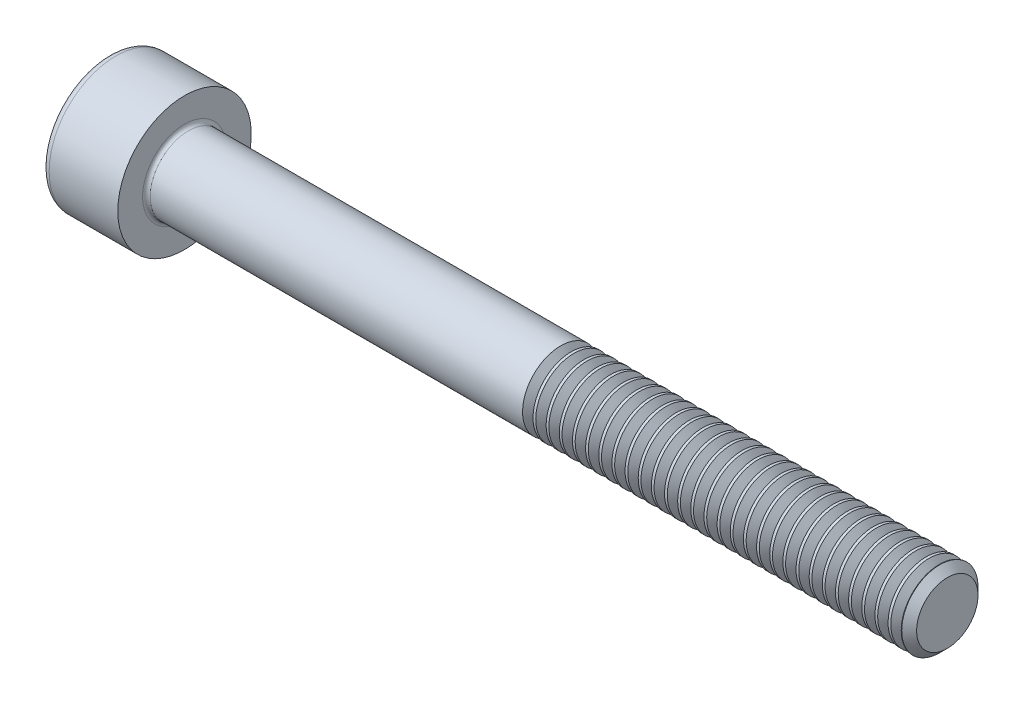
SolidWorks part; units mm, degrees
revolve "Base-Revolve" add sketch "BodySke"
sketch "BodySke" plane through (0, 0, 0) normal (0, 0, 1) x (1, 0, 0)
  line L0 (0, 0) -> (0, 3.5)
  line L1 (0, 3.5) -> (4, 3.5)
  line L2 (4, 3.5) -> (4, 2)
  line L3 (4, 2) -> (43.61, 2)
  line L4 (44, 1.61) -> (44, 0)
  line L5 (44, 0) -> (0, 0)
  line L6 (-31.75, 0) -> (127, 0) construction
  line L8 (44, 1.61) -> (43.61, 2)
  line L10 (44, -1.61) -> (43.61, -2) construction
  line L11 (4.7, 9.525) -> (4.7, 3.175) construction
  line L12 (24, 9.525) -> (24, 3.175) construction
  line L13 (-16, 9.525) -> (-16, 3.175) construction
cosmetic thread "ThreadCosmetic" [suppressed]
fillet "Fillet1" radius 0.2 1 edges at (4, 0, 2)
fillet "Fillet2" radius 0.4 1 edges at (0, 0, 3.5)
ref_plane "Plane1" through (0, 0, 0) normal (0, 0, 1) x (1, 0, 0)
ref_plane "Plane2" through (0, 0, 0) normal (0, 1, 0) x (1, 0, 0)
ref_plane "Plane3" through (0, 0, 0) normal (1, 0, 0) x (0, 0, -1)
sketch "Sketch2" plane through (0, 0, 0) normal (0, 0, 1) x (1, 0, 0)
  line L0 (0, 1.51) -> (2, 1.51)
  line L1 (2, 1.51) -> (2.8718, 0)
  line L2 (-31.75, 0) -> (127, 0) construction
  line L3 (2.8718, 0) -> (0, 0)
  line L4 (0, 0) -> (0, 1.51)
  line L6 (0, 0) -> (47.625, 0) construction
revolve "Hex-PreBroach" cut sketch "Sketch2" angle 360 about L6
sketch "Sketch3" plane through (0, 0, 0) normal (-1, 0, 0) x (0, 0.5, 0.866)
  line L0 (0.8718, 1.51) -> (-0.8718, 1.51)
  line L1 (-0.8718, 1.51) -> (-1.7436, 0)
  line L2 (0.8718, 1.51) -> (1.7436, 0)
  line L3 (0.8718, -1.51) -> (1.7436, 0)
  line L4 (0.8718, -1.51) -> (-0.8718, -1.51)
  line L5 (-0.8718, -1.51) -> (-1.7436, 0)
extrude "Hex" cut sketch "Sketch3" against normal blind 2
sketch "ThdSchSke" plane through (0, 0, 0) normal (0, 0, 1) x (1, 0, 0)
  line L0 (24, -1.61) -> (23.7269, -2)
  line L1 (24, -1.61) -> (24.2731, -2)
  line L2 (24.2731, -2) -> (24.2731, -2.5)
  line L3 (-3.175, 0) -> (5.1513, 0) construction
  line L4 (0, 3.1) -> (0, -3.1) construction
  line L5 (24.2731, -2.5) -> (23.7269, -2.5)
  line L6 (23.7269, -2.5) -> (23.7269, -2)
revolve "ThreadSchematic" cut sketch "ThdSchSke" angle 360 about L3
pattern_linear "ThdSchPat" count 29 spacing 0.6897 along (1, 0, 0) of "ThreadSchematic"
equation "\"D2@Sketch3\" = \"Hex_size@Sketch3\" / 2"
equation "\"D1@Sketch3\" = \"Hex_size@Sketch3\" / 2"
equation "\"D1@Sketch2\" = \"Hex_size@Sketch3\" / 2"
equation "\"Thread_minor@ThreadCosmetic\"  =  \"Minor_dia@BodySke\""
equation "\"Depth@Sketch2\" =  \"Key_eng@Hex\""
equation "\"Thread_length@ThreadCosmetic\" = ((sgn( (\"Length@BodySke\" - \"Advance@BodySke\" * 3.0) - \"Thread_nom@BodySke\" )-1)*( (\"Length@BodySke\" - \"Advance@BodySke\" * 3.0) - \"Thread_nom@BodySke\" ))/-2+ \"Thread_nom@BodySke\""
equation "\"Thread_minor@ThdSchSke\" = \"Minor_dia@BodySke\""
equation "\"Diameter@ThdSchSke\" = \"Diameter@BodySke\""
equation "\"Overcut@ThdSchSke\" = \"Diameter@BodySke\" * 1.25"
equation "\"Start@ThdSchSke\" = \"Head_ht@BodySke\" + \"Length@BodySke\" - \"Thread_length@ThreadCosmetic\"  '---Non-countersunk---"
equation "\"Num_threads@ThdSchPat\" = int( \"Thread_length@ThreadCosmetic\" / \"Advance@BodySke\" + 0.999 )  + 1"
equation "\"Advance@ThdSchPat\" = \"Thread_length@ThreadCosmetic\" /  (\"Num_threads@ThdSchPat\" - 1) 'relax it"
equation "\"Num_threads@ThdSchPat\" = \"Num_threads@ThdSchPat\" - sgn( \"Num_threads@ThdSchPat\" - 1) '---chamfered tips only---"
